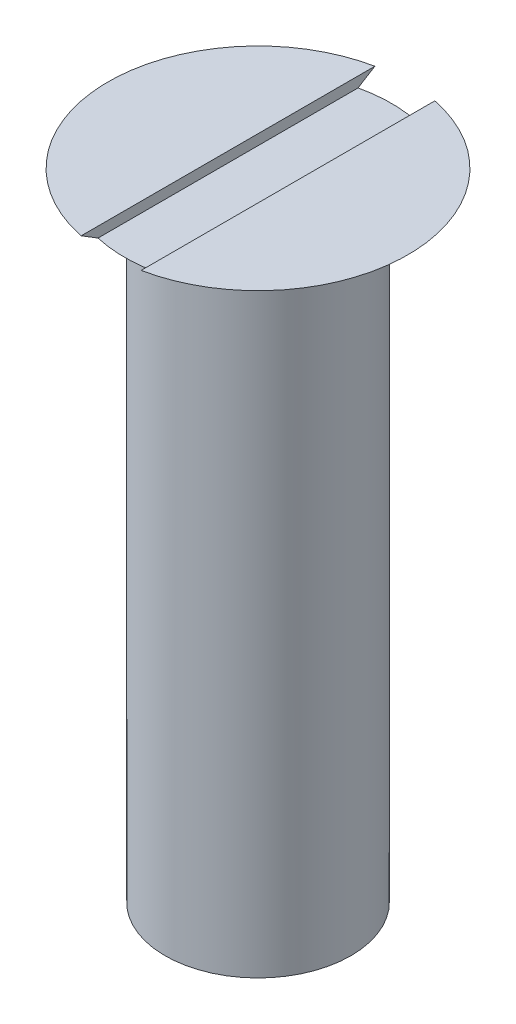
SolidWorks part; units mm, degrees
ref_plane "Front Plane" through (0, 0, 0) normal (0, 0, 1) x (1, 0, 0)
ref_plane "Top Plane" through (0, 0, 0) normal (0, 1, 0) x (1, 0, 0)
ref_plane "Right Plane" through (0, 0, 0) normal (1, 0, 0) x (0, 0, -1)
sketch "Sketch1" plane through (0, 0, 0) normal (0, 0, 1) x (1, 0, 0)
  line L0 (0, 0) -> (1.55, 0)
  line L1 (1.55, 0) -> (1.55, 10)
  line L2 (1.55, 10) -> (2.5, 10.6)
  line L3 (2.5, 10.6) -> (0, 10.6)
  line L4 (0, 0) -> (0, 10.6) construction
  line L5 (0, 0) -> (0, 10.6)
  dimension "D1" = 2.5
  dimension "D2" = 10
  dimension "D3" = 1.55
  dimension "D4" = 0.6
  dimension "D5" = 1.55
revolve "Revolve1" add sketch "Sketch1" angle 360 about L4
sketch "Sketch2" plane through (0, 0, 0) normal (0, 0, 1) x (1, 0, 0)
  line L0 (2.5, 10.6) -> (-2.5, 10.6) construction
  line L1 (-0.5, 10.4267) -> (0.5, 10.4267)
  line L2 (-0.5, 10.4267) -> (-0.5, 10.7733)
  line L3 (-0.5, 10.7733) -> (0.5, 10.7733)
  line L4 (0.5, 10.4267) -> (0.5, 10.7733)
  line L5 (-0.5, 10.4267) -> (0.5, 10.7733) construction
  line L6 (-0.5, 10.7733) -> (0.5, 10.4267) construction
  point P0 (0, 10.6)
  dimension "D1" = 1
extrude "Cut-Extrude1" cut sketch "Sketch2" against normal through all both and the other way through all
